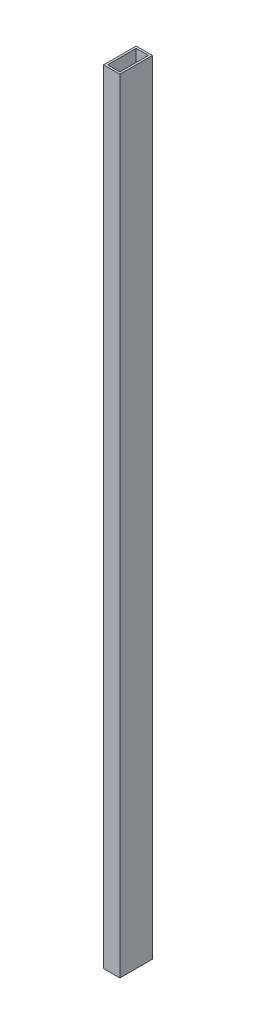
SolidWorks part; units mm, degrees
ref_plane "Front Plane" through (0, 0, 0) normal (0, 0, 1) x (1, 0, 0)
ref_plane "Top Plane" through (0, 0, 0) normal (0, 1, 0) x (1, 0, 0)
ref_plane "Right Plane" through (0, 0, 0) normal (1, 0, 0) x (0, 0, -1)
sketch "Sketch1" plane through (0, 0, 0) normal (0, 1, 0) x (1, 0, 0)
  line L1 (0, 0) -> (25.4, 0)
  line L2 (0, 0) -> (0, 50.8)
  line L3 (0, 50.8) -> (25.4, 50.8)
  line L4 (25.4, 0) -> (25.4, 50.8)
  line L5 (3.175, 47.625) -> (22.225, 47.625)
  line L6 (3.175, 47.625) -> (3.175, 3.175)
  line L7 (3.175, 3.175) -> (22.225, 3.175)
  line L8 (22.225, 47.625) -> (22.225, 3.175)
  dimension "D1" = 3.175
  dimension "D2" = 3.175
  dimension "D3" = 3.175
  dimension "D4" = 3.175
  dimension "D5" = 25.4
  dimension "D6" = 50.8
extrude "Boss-Extrude1" add sketch "Sketch1" along normal blind 1219.2
